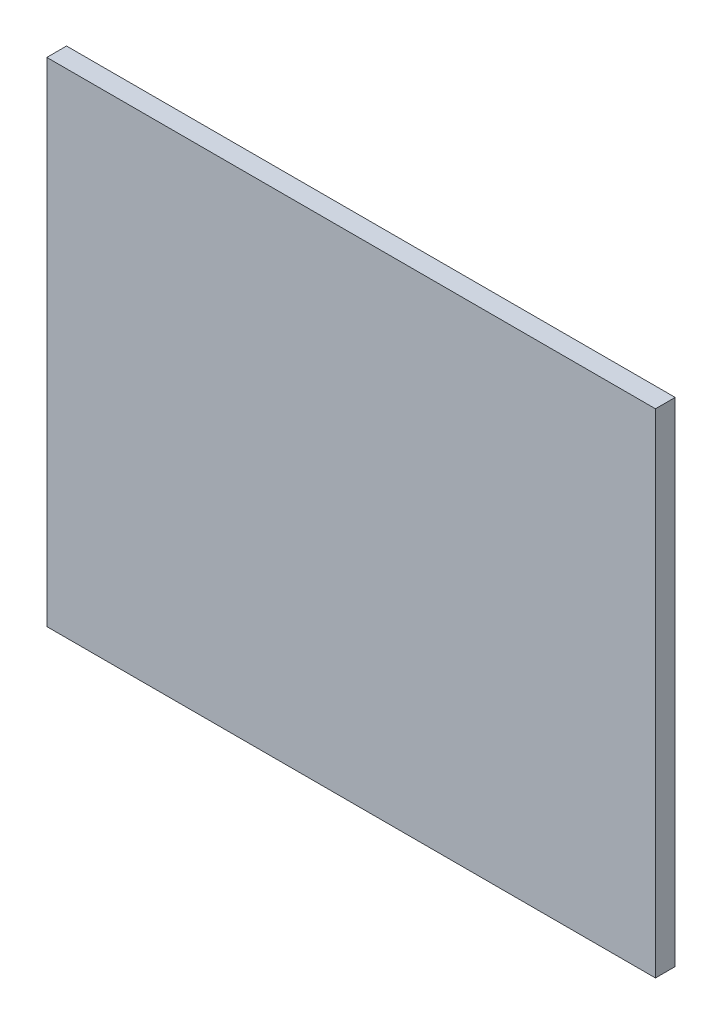
SolidWorks part; units mm, degrees
ref_plane "Front Plane" through (0, 0, 0) normal (0, 0, 1) x (1, 0, 0)
ref_plane "Top Plane" through (0, 0, 0) normal (0, 1, 0) x (1, 0, 0)
ref_plane "Right Plane" through (0, 0, 0) normal (1, 0, 0) x (0, 0, -1)
sketch "Sketch2" plane through (0, 0, 0) normal (0, 0, 1) x (1, 0, 0)
  line L1 (-19.2883, 18.3076) -> (27.0117, 18.3076)
  line L2 (-19.2883, 18.3076) -> (-19.2883, -19.1924)
  line L3 (-19.2883, -19.1924) -> (27.0117, -19.1924)
  line L4 (27.0117, 18.3076) -> (27.0117, -19.1924)
  dimension "D1" = 37.5
  dimension "D2" = 46.3
extrude "Boss-Extrude1" add sketch "Sketch2" along normal blind 1.5
